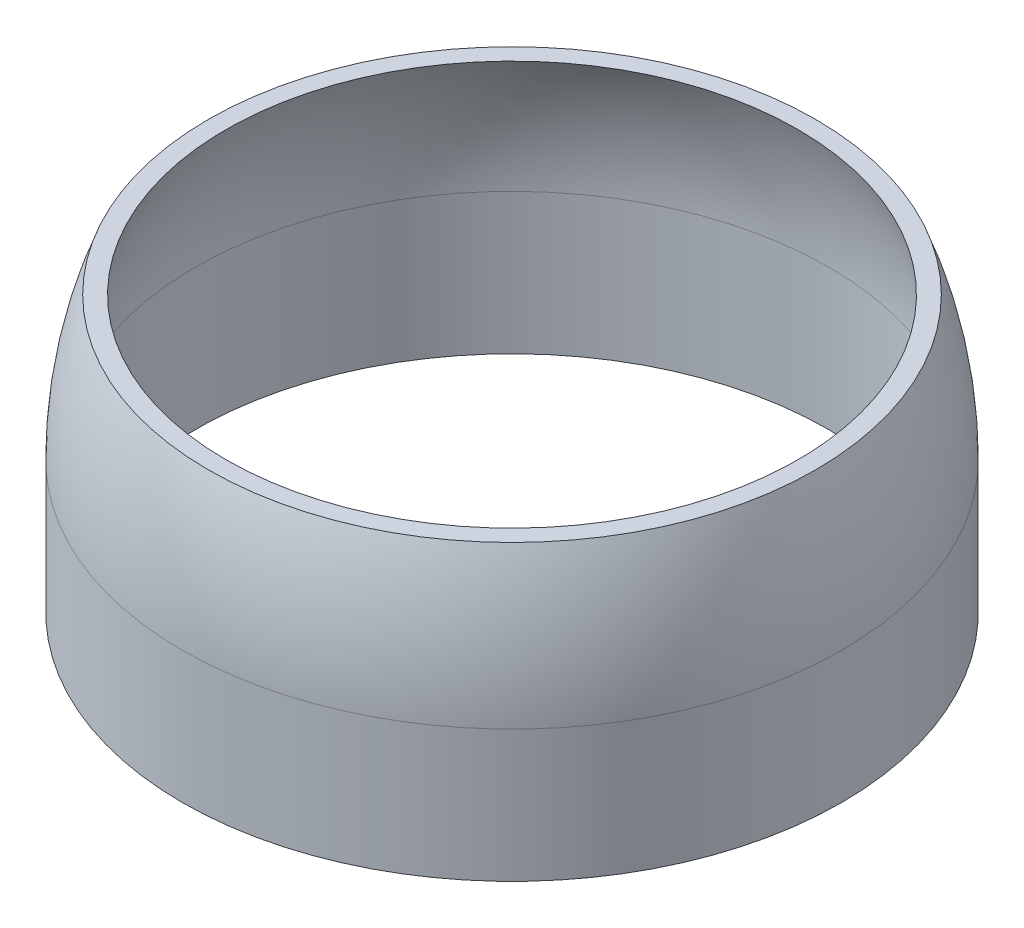
SolidWorks part; units mm, degrees
ref_plane "Front Plane" through (0, 0, 0) normal (0, 0, 1) x (1, 0, 0)
ref_plane "Top Plane" through (0, 0, 0) normal (0, 1, 0) x (1, 0, 0)
ref_plane "Right Plane" through (0, 0, 0) normal (1, 0, 0) x (0, 0, -1)
sketch "Sketch1" plane through (0, 0, 0) normal (0, 0, 1) x (1, 0, 0)
  line L4 (0, 0) -> (0, 33.8642) construction
  line L5 (-23.5, 0) -> (-23.5, 19) construction
  line L6 (-23.625, 12.5) -> (-23.625, 6.5) construction
  line L7 (-23.625, 9.5) -> (-23.5, 9.5) construction
  line L8 (-26, 12.5) -> (-26, 6.5) construction
  line L9 (-26, 12.5) -> (-23.625, 12.5) construction
  line L10 (-26, 6.5) -> (-23.625, 6.5) construction
  line L11 (-23.625, 15.5) -> (-26, 15.5) construction
  line L12 (-23.625, 9.5) -> (-26, 9.5) construction
  line L13 (-24, 9.5) -> (-26, 9.5) construction
  line L14 (-26, 9.5) -> (-26, -8.5) construction
  line L15 (-26, -8.5) -> (-32, -8.5) construction
  line L16 (-30, 31) -> (-24, 31) construction
  line L17 (-24, 31) -> (-24, 9.5) construction
  line L18 (-26, -8.5) -> (0, -8.5) construction
  line L19 (0, -8.5) -> (0, -6) construction
  line L20 (23.625, 9.5) -> (23.5, 9.5) construction
  line L21 (23.625, 9.5) -> (26, 9.5) construction
  line L22 (23.625, 12.5) -> (23.625, 6.5) construction
  line L23 (23.5, 0) -> (23.5, 19) construction
  line L24 (24, 31) -> (24, 9.5) construction
  line L25 (23.625, 15.5) -> (26, 15.5) construction
  line L26 (26, 12.5) -> (26, 6.5) construction
  line L27 (26, 6.5) -> (23.625, 6.5) construction
  line L28 (26, 9.5) -> (26, -8.5) construction
  line L29 (26, -8.5) -> (32, -8.5) construction
  line L30 (30, 31) -> (24, 31) construction
  line L31 (0, -30.5) -> (-37.5, -30.5) construction
  line L32 (-27.4866, 2.7599) -> (-25.1347, 3.0904) construction
  line L33 (-25.399, -12.0942) -> (0.3479, -8.4757) construction
  line L34 (-34.8574, 26.4647) -> (-28.9158, 27.2998) construction
  line L36 (20.4029, 18.5787) -> (22.7547, 18.9093) construction
  line L37 (23.5898, 12.9677) -> (26.0949, -4.8572) construction
  line L39 (21.2379, 12.6371) -> (23.5898, 12.9677) construction
  line L40 (20.8204, 15.6079) -> (21.6554, 9.6663) construction
  line L41 (22.4363, 3.2122) -> (19.792, 22.0273) construction
  line L42 (-28.3217, 8.7015) -> (-25.9698, 9.032) construction
  line L43 (-25.399, -12.0942) -> (-31.3406, -12.9292) construction
  line L44 (-28.9158, 27.2998) -> (-25.9236, 6.009) construction
  line L45 (-0.835, -0.0584) -> (-5.548, 33.4763) construction
  line L46 (-25.9698, 9.032) -> (-25.1347, 3.0904) construction
  line L47 (26.0949, -4.8572) -> (32.0365, -4.0221) construction
  line L48 (-25.5523, 6.0612) -> (-27.9042, 5.7307) construction
  line L49 (-27.9042, 5.7307) -> (-25.399, -12.0942) construction
  line L50 (24.0073, 9.9969) -> (21.6554, 9.6663) construction
  line L51 (-25.5523, 6.0612) -> (-25.4285, 6.0786) construction
  line L52 (-24.1063, -3.329) -> (-26.7506, 15.4861) construction
  line L54 (24.5586, 34.8151) -> (18.617, 33.9801) construction
  line L55 (-26.3873, 12.0028) -> (-28.7392, 11.6723) construction
  line L56 (21.2379, 12.6371) -> (21.1141, 12.6197) construction
  line L58 (-25.9236, 6.009) -> (-27.9042, 5.7307) construction
  line L59 (23.1723, 15.9385) -> (24.0073, 9.9969) construction
  line L60 (-28.3217, 8.7015) -> (-27.4866, 2.7599) construction
  line L61 (18.617, 33.9801) -> (21.6093, 12.6893) construction
  line L62 (0.3479, -8.4757) -> (0, -6) construction
  line L63 (25.5523, 6.0612) -> (27.9042, 5.7307) construction
  line L64 (24.1063, -3.329) -> (26.7506, 15.4861) construction
  line L65 (25.9698, 9.032) -> (25.1347, 3.0904) construction
  line L66 (-22.4363, 3.2122) -> (-19.792, 22.0273) construction
  line L67 (-23.1723, 15.9385) -> (-20.8204, 15.6079) construction
  line L68 (-23.5898, 12.9677) -> (-26.0949, -4.8572) construction
  line L69 (-26.0949, -4.8572) -> (-32.0365, -4.0221) construction
  line L70 (-20.4029, 18.5787) -> (-22.7547, 18.9093) construction
  line L71 (-24.5586, 34.8151) -> (-18.617, 33.9801) construction
  line L72 (25.399, -12.0942) -> (31.3406, -12.9292) construction
  line L73 (27.4866, 2.7599) -> (25.1347, 3.0904) construction
  line L74 (0.835, -0.0584) -> (5.548, 33.4763) construction
  line L75 (-0.3479, -8.4757) -> (0, -6) construction
  line L76 (-21.2379, 12.6371) -> (-21.1141, 12.6197) construction
  line L77 (-21.6093, 12.6893) -> (-23.5898, 12.9677) construction
  line L78 (-21.2379, 12.6371) -> (-23.5898, 12.9677) construction
  line L79 (34.8574, 26.4647) -> (28.9158, 27.2998) construction
  line L80 (-20.8204, 15.6079) -> (-21.6554, 9.6663) construction
  line L81 (-23.1723, 15.9385) -> (-24.0073, 9.9969) construction
  line L82 (25.5523, 6.0612) -> (25.4285, 6.0786) construction
  line L83 (-24.0073, 9.9969) -> (-21.6554, 9.6663) construction
  line L84 (-26.0949, -4.8572) -> (-0.3479, -8.4757) construction
  line L85 (26.3873, 12.0028) -> (28.7392, 11.6723) construction
  line L86 (28.9158, 27.2998) -> (25.9236, 6.009) construction
  line L87 (27.9042, 5.7307) -> (25.399, -12.0942) construction
  line L88 (-18.617, 33.9801) -> (-21.6093, 12.6893) construction
  line L89 (28.3217, 8.7015) -> (27.4866, 2.7599) construction
  line L94 (-36, -21.5) -> (0, -21.5) construction
  line L95 (-36, -21.5) -> (-36, -15.5) construction
  line L96 (-37.5, -40.8) -> (0, -40.8) construction
  line L101 (0, -43.8) -> (-27.5, -43.8) construction
  line L102 (-36, -30.5) -> (-37.5, -30.5)
  line L104 (-36, -30.5) -> (-36, -14.5)
  line L105 (-32.5296, 0.7825) -> (-34.5296, 0.7825)
  line L107 (-37.5, -30.5) -> (-37.5, -15.5)
  arc A0 (-32, -8.5) -> (-30, 31) centre (-87.575, 14.1146) ccw construction
  arc A1 (32, -8.5) -> (30, 31) centre (87.575, 14.1146) cw construction
  arc A2 (32.0365, -4.0221) -> (24.5586, 34.8151) centre (83.9233, 26.1069) cw construction
  arc A3 (-31.3406, -12.9292) -> (-34.8574, 26.4647) centre (-89.5221, 1.7307) ccw construction
  arc A4 (-32.0365, -4.0221) -> (-24.5586, 34.8151) centre (-83.9233, 26.1069) ccw construction
  arc A5 (31.3406, -12.9292) -> (34.8574, 26.4647) centre (89.5221, 1.7307) cw construction
  arc A8 (-32.5296, 0.7825) -> (-36, -14.5) centre (-0.615, -14.5) ccw
  arc A9 (-34.5296, 0.7825) -> (-37.5, -15.5) centre (8.6125, -15.5) ccw
  point P43 (-36, -30.5)
  point P118 (-29.5296, 0.7825)
  point P119 (-29.6011, -1.3458)
  point P120 (-29.6011, -1.3458)
  dimension "D10" = 16
  dimension "D2" = 9
  dimension "D3" = 6
  dimension "D4" = 10.3
  dimension "D5" = 3
  dimension "D6" = 27.5
  dimension "D8" = 3
  dimension "D9" = 2
  dimension "D12" = 15
  dimension "D14" = 22
  dimension "D15" = 37.5
  dimension "D16" = 1.5
revolve "Revolve1" add sketch "Sketch1" angle 360 about L4
